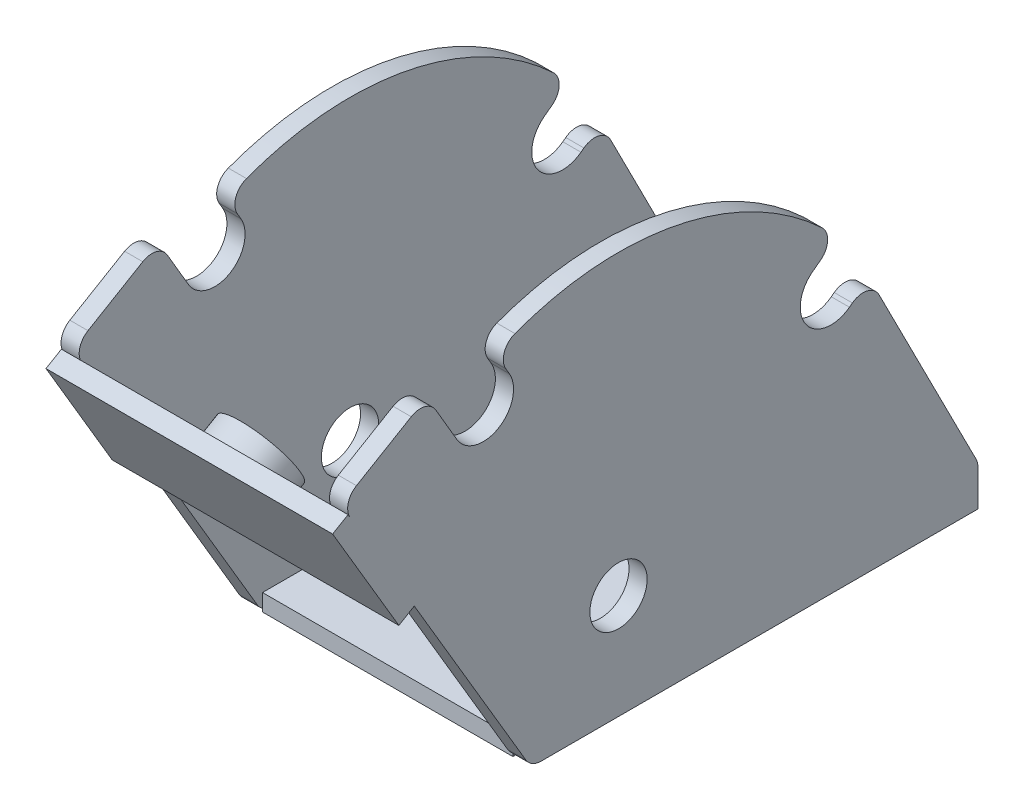
SolidWorks part; units mm, degrees
ref_plane "Front Plane" through (0, 0, 0) normal (0, 0, 1) x (1, 0, 0)
ref_plane "Top Plane" through (0, 0, 0) normal (0, 1, 0) x (1, 0, 0)
ref_plane "Right Plane" through (0, 0, 0) normal (1, 0, 0) x (0, 0, -1)
sketch "Sketch1" plane through (0, 0, 0) normal (0, 1, 0) x (1, 0, 0)
  line L0 (0, -1000) -> (0, 49000) construction
  line L1 (-17.78, -31.75) -> (17.78, -31.75)
  line L2 (-17.78, -31.75) -> (-17.78, 31.75)
  line L3 (-17.78, 31.75) -> (17.78, 31.75)
  line L4 (17.78, -31.75) -> (17.78, 31.75)
  line L5 (-17.78, -31.75) -> (17.78, 31.75) construction
  line L6 (-17.78, 31.75) -> (17.78, -31.75) construction
  circle A0 centre (-11.0109, 22.225) radius 3.0734
  circle A1 centre (-11.0109, -18.288) radius 3.0734
  circle A2 centre (11.0109, -18.288) radius 3.0734
  circle A3 centre (11.0109, 22.225) radius 3.0734
  point P0 (0, 0)
  dimension "D3" = 6.1468
  dimension "D1" = 35.56
  dimension "D2" = 63.5
  dimension "D4" = 13.462
  dimension "D5" = 6.7691
  dimension "D6" = 9.525
extrude "Boss-Extrude1" add sketch "Sketch1" along normal blind 2.4003
sketch "Sketch2" plane through (17.78, 0, 0) normal (1, 0, 0) x (0, 0, -1)
  line L0 (31.75, 0) -> (31.75, 5.1191)
  line L1 (31.75, 0) -> (-30.2995, 0)
  line L2 (-32.4871, 1.2492) -> (-57.4371, 43.5324)
  line L3 (-35.3361, 50.8042) -> (-34.8166, 49.9161)
  line L4 (31.4742, 6.2702) -> (17.6936, 33.377)
  line L5 (-45.2777, 50.696) -> (-42.271, 45.5558)
  line L6 (-56.5403, 47.0108) -> (-48.761, 51.6011)
  line L7 (-42.271, 45.5558) -> (-34.8166, 49.9161) construction
  line L8 (9.3783, 41.7831) -> (8.2564, 40.944)
  line L9 (13.908, 34.2599) -> (13.4898, 33.9471)
  line L10 (8.2564, 40.944) -> (13.4898, 33.9471) construction
  line L11 (-38.5438, 47.7359) -> (-19.3166, 14.8653) construction
  line L12 (-19.3166, 14.8653) -> (10.8731, 37.4455) construction
  arc A0 (-34.0281, 54.4677) -> (9.5952, 45.6691) centre (-19.3166, 14.8653) cw
  circle A1 centre (-19.3166, 14.8653) radius 4.0704
  arc A2 (-42.271, 45.5558) -> (-34.8166, 49.9161) centre (-38.5438, 47.7359) ccw
  arc A3 (8.2564, 40.944) -> (13.4898, 33.9471) centre (10.8731, 37.4455) ccw
  arc A4 (-30.2995, 0) -> (-32.4871, 1.2492) centre (-30.2995, 2.54) cw
  arc A5 (31.75, 5.1191) -> (31.4742, 6.2702) centre (29.21, 5.1191) ccw
  arc A6 (17.6936, 33.377) -> (13.908, 34.2599) centre (15.4294, 32.2259) ccw
  arc A7 (9.5952, 45.6691) -> (9.3783, 41.7831) centre (7.857, 43.8171) cw
  arc A8 (-35.3361, 50.8042) -> (-34.0281, 54.4677) centre (-33.1436, 52.0867) cw
  arc A9 (-45.2777, 50.696) -> (-48.761, 51.6011) centre (-47.4701, 49.4136) ccw
  arc A10 (-57.4371, 43.5324) -> (-56.5403, 47.0108) centre (-55.2495, 44.8232) cw
  point P20 (-31.75, 0)
  point P23 (31.75, 5.7277)
  point P26 (16.3255, 36.068)
  point P33 (-46.565, 52.8969)
  point P36 (-58.7279, 45.72)
  dimension "D2" = 8.1407
  dimension "D12" = 42.2465
  dimension "D15" = 2.54
  dimension "D1" = 14.8654
  dimension "D3" = 18.2626
  dimension "D4" = 53.086
  dimension "D5" = 45.72
  dimension "D6" = 14.1224
  dimension "D7" = 8.636
  dimension "D8" = 38.0809
  dimension "D9" = 34.036
  dimension "D10" = 5.7277
  dimension "D11" = 36.068
  dimension "D13" = 8.7376
  dimension "D14" = 37.6999
extrude "Boss-Extrude2" add sketch "Sketch2" along normal blind 2.5781
ref_plane "Plane1" through (0, 0, 0) normal (-1, 0, 0) x (0, 0, 1)
mirror "Mirror1" about plane through (0, 0, 0) normal (-1, 0, 0) of "Boss-Extrude2"
sketch "Sketch3" plane through (0, -13.8962, 23.5503) normal (0, -0.5082, 0.8612) x (1, 0, 0)
  line L0 (-20.3581, 66.6811) -> (-20.3581, 17.5855) construction
  line L1 (-20.3581, 48.7585) -> (20.3581, 48.7585)
  line L2 (-20.3581, 48.7585) -> (-20.3581, 67.2751)
  line L3 (-20.3581, 67.2751) -> (20.3581, 67.2751)
  line L4 (20.3581, 48.7585) -> (20.3581, 67.2751)
  line L5 (20.3581, 66.6811) -> (20.3581, 17.5855) construction
  line L6 (-17.78, 18.2023) -> (17.78, 18.2023) construction
  dimension "D1" = 18.5166
  dimension "D2" = 30.5562
extrude "Boss-Extrude3" add sketch "Sketch3" along normal blind 2.54
sketch "Sketch4" plane through (0, -13.8962, 23.5503) normal (0, 0.5082, -0.8612) x (-1, 0, 0)
  line L0 (-20.3581, 67.2751) -> (20.3581, 67.2751) construction
  line L1 (-20.3581, 48.7585) -> (-20.3581, 67.2751) construction
  circle A0 centre (0, 58.0168) radius 5.5626
  point P4 (0, 67.2751)
  point P7 (-20.3581, 58.0168)
  dimension "D1" = 11.1252
extrude "Boss-Extrude4" add sketch "Sketch4" along normal blind 3.7846
